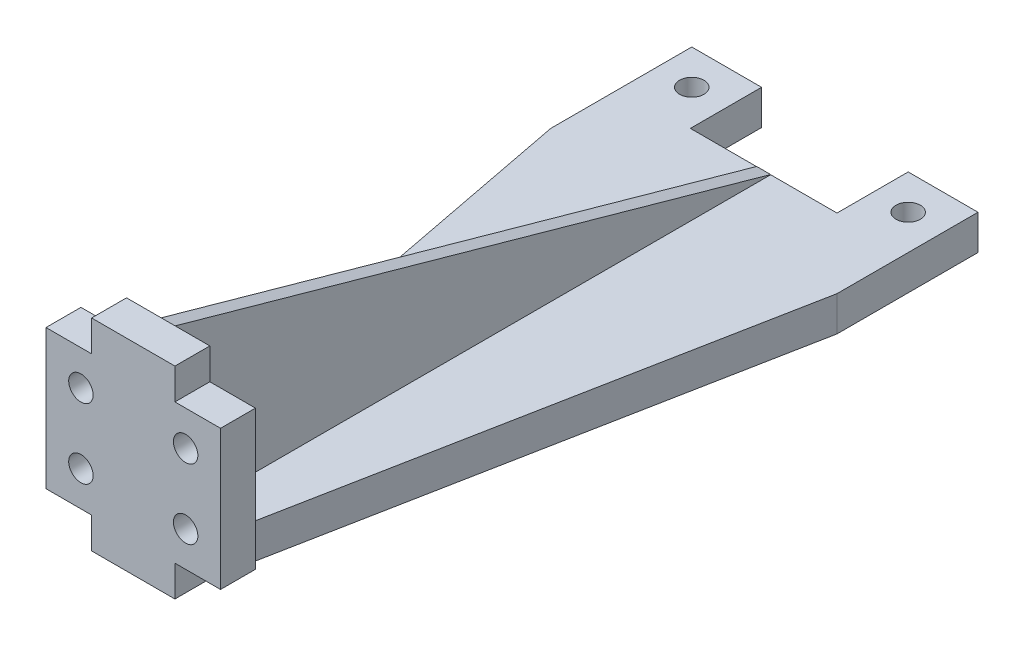
SolidWorks part; units mm, degrees
ref_plane "Front Plane" through (0, 0, 0) normal (0, 0, 1) x (1, 0, 0)
ref_plane "Top Plane" through (0, 0, 0) normal (0, 1, 0) x (1, 0, 0)
ref_plane "Right Plane" through (0, 0, 0) normal (1, 0, 0) x (0, 0, -1)
sketch "Sketch1" plane through (0, 0, 0) normal (0, 1, 0) x (1, 0, 0)
  line L1 (0, 0) -> (41, 0)
  line L2 (0, 0) -> (0, 100.5)
  line L3 (0, 100.5) -> (41, 100.5)
  line L4 (41, 0) -> (41, 100.5)
  dimension "D1" = 41
  dimension "D2" = 100.5
extrude "Boss-Extrude1" add sketch "Sketch1" along normal blind 5
sketch "Sketch2" plane through (0, 5, 0) normal (0, 1, 0) x (1, 0, 0)
  line L1 (0, 100.5) -> (10, 100.5) construction
  line L2 (0, 100.5) -> (0, 90.3) construction
  line L3 (0, 90.3) -> (10, 90.3) construction
  line L4 (10, 100.5) -> (10, 90.3) construction
  line L5 (41, 100.5) -> (31, 100.5) construction
  line L6 (41, 100.5) -> (41, 90.3) construction
  line L7 (41, 90.3) -> (31, 90.3) construction
  line L8 (31, 100.5) -> (31, 90.3) construction
  line L9 (10, 100.5) -> (31, 100.5)
  line L10 (10, 100.5) -> (10, 90.3)
  line L11 (10, 90.3) -> (31, 90.3)
  line L12 (31, 100.5) -> (31, 90.3)
  dimension "D1" = 10.2
  dimension "D3" = 10
  dimension "D4" = 10
extrude "Cut-Extrude1" cut sketch "Sketch2" against normal through all
sketch "Sketch9" plane through (0, 5, 0) normal (0, 1, 0) x (1, 0, 0)
  line L1 (0, 100.5) -> (5, 100.5) construction
  line L2 (0, 100.5) -> (0, 95.5) construction
  line L3 (0, 95.5) -> (5, 95.5) construction
  line L4 (5, 100.5) -> (5, 95.5) construction
  line L5 (31, 100.5) -> (36, 100.5) construction
  line L6 (31, 100.5) -> (31, 95.5) construction
  line L7 (31, 95.5) -> (36, 95.5) construction
  line L8 (36, 100.5) -> (36, 95.5) construction
  circle A0 centre (5, 95.5) radius 1.75
  circle A1 centre (36, 95.5) radius 1.75
  dimension "D3" = 3.5
  dimension "D4" = 3.5
  dimension "D1" = 5
  dimension "D2" = 5
extrude "Cut-Extrude4" cut sketch "Sketch9" against normal through all
sketch "Sketch11" plane through (0, 5, 0) normal (0, 1, 0) x (1, 0, 0)
  line L0 (20.5, 90.3) -> (20.5, 0) construction
  line L1 (10, 90.3) -> (31, 90.3) construction
  line L2 (0, 0) -> (41, 0) construction
  line L3 (15.5, 0) -> (25.5, 0) construction
  line L4 (15.5, 0) -> (0, 80.3)
  line L5 (0, 100.5) -> (0, 0) construction
  line L6 (25.5, 0) -> (41, 80.3)
  line L7 (41, 0) -> (41, 100.5) construction
  line L8 (0, 80.3) -> (0, 0)
  line L9 (0, 0) -> (15.5, 0)
  line L10 (41, 80.3) -> (41, 0)
  line L11 (41, 0) -> (25.5, 0)
  point P8 (20.5, 0)
  dimension "D1" = 10
  dimension "D2" = 10
extrude "Cut-Extrude5" cut sketch "Sketch11" against normal through all
sketch "Slider Reference" plane through (0, 0, 0) normal (0, 0, 1) x (1, 0, 0)
  line L0 (15.5, 0) -> (25.5, 0) construction
  line L1 (8, 0) -> (33, 0) construction
  line L2 (8, 0) -> (8, 28.9) construction
  line L3 (8, 28.9) -> (33, 28.9) construction
  line L4 (33, 0) -> (33, 28.9) construction
  line L6 (13, 19.45) -> (28, 19.45) construction
  line L7 (13, 19.45) -> (13, 9.45) construction
  line L8 (13, 9.45) -> (28, 9.45) construction
  line L9 (28, 19.45) -> (28, 9.45) construction
  line L10 (8, 24.45) -> (33, 24.45) construction
  line L11 (8, 24.45) -> (8, 4.45) construction
  line L12 (8, 4.45) -> (33, 4.45) construction
  line L13 (33, 24.45) -> (33, 4.45) construction
  point P5 (20.5, 0)
  point P8 (20.5, 0)
  point P13 (13, 14.45)
  point P14 (8, 14.45)
  point P15 (20.5, 19.45)
  point P16 (20.5, 28.9)
  dimension "D1" = 28.9
  dimension "D2" = 25
  dimension "D3" = 10
  dimension "D4" = 15
  dimension "D5" = 5
  dimension "D6" = 5
sketch "Sketch12" plane through (0, 5, 0) normal (0, 1, 0) x (1, 0, 0)
  line L0 (25.5, 0) -> (15.5, 0)
  line L1 (15.5, 0) -> (14.5349, 5)
  line L2 (15.5, 0) -> (0, 80.3) construction
  line L3 (14.5349, 5) -> (26.4651, 5)
  line L4 (41, 80.3) -> (25.5, 0) construction
  line L5 (26.4651, 5) -> (25.5, 0)
  dimension "D1" = 5
extrude "Boss-Extrude4" add sketch "Sketch12" along normal up to vertex (23.9 mm away) up to point (8, 28.9, 0)
sketch "Sketch16" plane through (0, 5, 0) normal (0, 1, 0) x (1, 0, 0)
  line L0 (10, 90.3) -> (31, 90.3) construction
  line L1 (19.5, 90.3) -> (21.5, 90.3)
  line L2 (19.5, 90.3) -> (19.5, 5)
  line L3 (19.5, 5) -> (21.5, 5)
  line L4 (21.5, 90.3) -> (21.5, 5)
  line L5 (26.4651, 5) -> (14.5349, 5) construction
  point P6 (20.5, 90.3)
  point P7 (20.5, 90.3)
  dimension "D1" = 2
extrude "Boss-Extrude5" add sketch "Sketch16" along normal up to surface (23.9 mm away) up to face at (20.5, 28.9, -2.5)
sketch "Sketch17" plane through (19.5, 0, 0) normal (-1, 0, 0) x (0, 0, 1)
  line L0 (-90.4, 5) -> (-5, 28.9)
  line L1 (-100.5, 5) -> (-80.3, 5) construction
  line L2 (-5, 28.9) -> (-90.3, 28.9)
  line L3 (-90.3, 28.9) -> (-90.4, 5)
  line L4 (-90.3, 28.9) -> (-90.3, 5) construction
extrude "Cut-Extrude8" cut sketch "Sketch17" against normal through all
sketch "Sketch23" plane through (0, 28.9, 0) normal (0, 1, 0) x (1, 0, 0)
  line L0 (26.4651, 5) -> (33, 5)
  line L1 (33, 5) -> (33, 0)
  line L2 (8, 0) -> (33, 0) construction
  line L3 (33, 0) -> (25.5, 0)
  line L4 (25.5, 0) -> (26.4651, 5)
  line L5 (14.5349, 5) -> (8, 5)
  line L6 (8, 5) -> (8, 0)
  line L7 (8, 0) -> (33, 0) construction
  line L8 (8, 0) -> (15.5, 0)
  line L9 (15.5, 0) -> (14.5349, 5)
extrude "Boss-Extrude6" add sketch "Sketch23" against normal up to surface (28.9 mm away) up to face at (20.5, 0, -74.32)
sketch "Sketch25" plane through (0, 0, -5) normal (0, 0, -1) x (-1, 0, 0)
  line L0 (-8, 4.45) -> (-33, 4.45) construction
  line L1 (-8, 4.45) -> (-14.5349, 4.45)
  line L3 (-8, 4.45) -> (-8, 0)
  line L4 (-8, 0) -> (-14.5349, 0)
  line L6 (-14.5349, 4.45) -> (-14.5349, 0)
  line L8 (-26.4651, 0) -> (-33, 0)
  line L9 (-26.4651, 0) -> (-26.4651, 4.45)
  line L10 (-26.4651, 4.45) -> (-33, 4.45)
  line L11 (-33, 0) -> (-33, 4.45)
  line L12 (-8, 24.45) -> (-33, 24.45) construction
  line L13 (-8, 28.9) -> (-14.5349, 28.9)
  line L14 (-8, 28.9) -> (-8, 24.45)
  line L15 (-8, 24.45) -> (-14.5349, 24.45)
  line L16 (-14.5349, 28.9) -> (-14.5349, 24.45)
  line L18 (-33, 28.9) -> (-26.4651, 28.9)
  line L19 (-33, 28.9) -> (-33, 24.45)
  line L20 (-33, 24.45) -> (-26.4651, 24.45)
  line L21 (-26.4651, 28.9) -> (-26.4651, 24.45)
extrude "Cut-Extrude9" cut sketch "Sketch25" against normal through all
sketch "Sketch26" plane through (0, 0, 0) normal (0, 0, 1) x (1, 0, 0)
  circle A0 centre (13, 19.45) radius 1.75
  circle A1 centre (28, 19.45) radius 1.75
  circle A2 centre (13, 9.45) radius 1.75
  circle A3 centre (28, 9.45) radius 1.75
  dimension "D1" = 3.5
extrude "Cut-Extrude10" cut sketch "Sketch26" against normal through all
